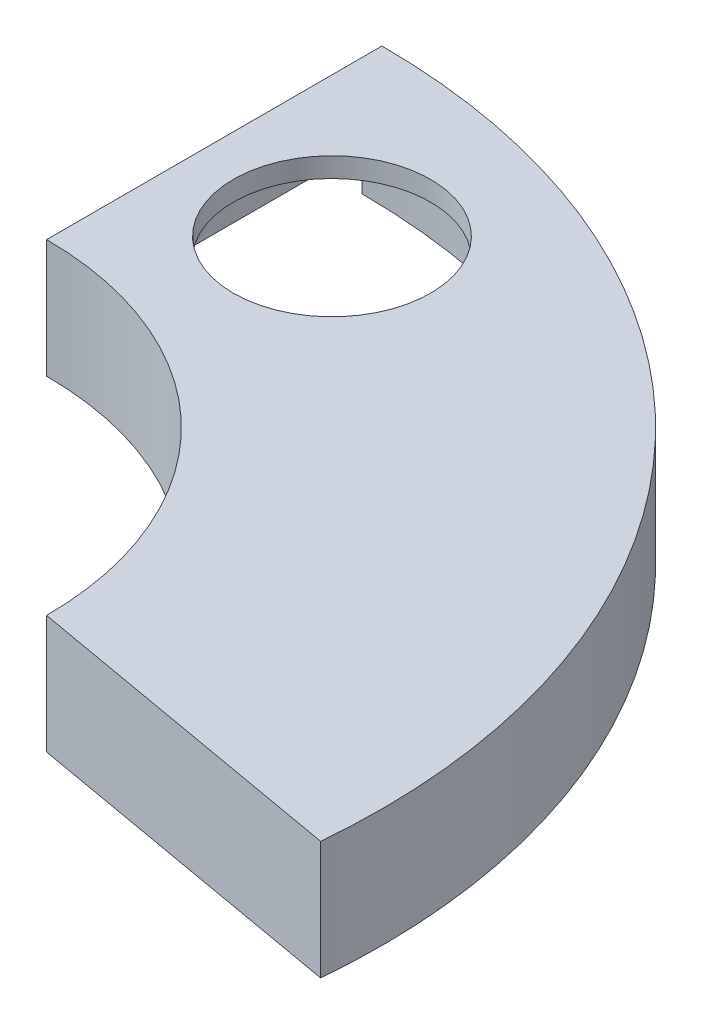
SolidWorks part; units mm, degrees
material "AISI 316 Chapa de acero inoxidable (SS)"
ref_plane "Alzado" through (0, 0, 0) normal (0, 0, 1) x (1, 0, 0)
ref_plane "Planta" through (0, 0, 0) normal (0, 1, 0) x (1, 0, 0)
ref_plane "Vista lateral" through (0, 0, 0) normal (1, 0, 0) x (0, 0, -1)
sketch "Croquis1" plane through (0, 0, 0) normal (0, 1, 0) x (1, 0, 0)
  line L0 (0, 165) -> (0, 335)
  line L1 (165, 0) -> (333.6771, -29.7423)
  arc A0 (333.6771, -29.7423) -> (0, 335) centre (0, 0) ccw
  arc A1 (165, 0) -> (0, 165) centre (0, 0) ccw
  circle A2 centre (70.8774, 238.7962) radius 50
  dimension "D1" = 670
  dimension "D2" = 330
  dimension "D4" = 100
  dimension "D3" = 100
extrude "Saliente-Extruir1" add sketch "Croquis1" along normal blind 10
sketch "Croquis2" plane through (0, 0, 0) normal (0, -1, 0) x (1, 0, 0)
  line L4 (10, -174.7141) -> (10, -324.8461)
  line L5 (324.5028, 17.9704) -> (174.797, -8.4268)
  line L6 (10, -174.7141) -> (10, -324.8461)
  line L7 (324.5028, 17.9704) -> (174.797, -8.4268)
  line L8 (0, -165) -> (0, -335)
  line L9 (333.6771, 29.7423) -> (165, 0)
  line L10 (0, -165) -> (0, -335)
  line L11 (333.6771, 29.7423) -> (165, 0)
  arc A4 (10, -174.7141) -> (174.797, -8.4268) centre (0, 0) ccw
  arc A5 (10, -324.8461) -> (324.5028, 17.9704) centre (0, 0) ccw
  arc A6 (10, -174.7141) -> (174.797, -8.4268) centre (0, 0) ccw
  arc A7 (10, -324.8461) -> (324.5028, 17.9704) centre (0, 0) ccw
  arc A8 (0, -165) -> (165, 0) centre (0, 0) ccw
  arc A9 (0, -335) -> (333.6771, 29.7423) centre (0, 0) ccw
  arc A10 (0, -165) -> (165, 0) centre (0, 0) ccw
  arc A11 (0, -335) -> (333.6771, 29.7423) centre (0, 0) ccw
  arc M9 (165, 0) -> (0, -165) centre (0, 0) cw
  line M10 (0, -165) -> (0, -335)
  arc M11 (0, -335) -> (333.6771, 29.7423) centre (0, 0) ccw
  line M12 (333.6771, 29.7423) -> (165, 0)
  dimension "D1" = 10
  dimension "D2" = 0
extrude "Saliente-Extruir2" add sketch "Croquis2" along normal blind 50 contours A7 L6 A6 L7 M12 M9 M10 M11 | A10 L11 A11 L10
sketch "Croquis3" plane through (0, -50, 0) normal (0, -1, 0) x (1, 0, 0)
  line L4 (324.5028, 17.9704) -> (174.797, -8.4268)
  line L5 (10, -174.7141) -> (10, -324.8461)
  line L6 (324.5028, 17.9704) -> (174.797, -8.4268)
  line L7 (10, -174.7141) -> (10, -324.8461)
  line L8 (333.6771, 29.7423) -> (165, 0)
  line L9 (0, -165) -> (0, -335)
  line L10 (333.6771, 29.7423) -> (165, 0)
  line L11 (0, -175) -> (0, -325)
  arc A2 (0, -175) -> (10, -174.7141) centre (0, 0) ccw
  arc A3 (0, -325) -> (10, -324.8461) centre (0, 0) ccw
  arc A4 (10, -174.7141) -> (174.797, -8.4268) centre (0, 0) ccw
  arc A5 (10, -324.8461) -> (324.5028, 17.9704) centre (0, 0) ccw
  arc A8 (0, -165) -> (165, 0) centre (0, 0) ccw
  arc A9 (0, -335) -> (333.6771, 29.7423) centre (0, 0) ccw
  arc A12 (324.5028, 17.9704) -> (323.7166, 28.8545) centre (0, 0) ccw
  arc A13 (174.797, -8.4268) -> (175, 0) centre (0, 0) ccw
  line M10 (10, -324.8461) -> (10, -174.7141)
  line M15 (0, -165) -> (0, -335)
  dimension "D1" = 10
  dimension "D2" = 0
extrude "Cortar-Extruir1" cut sketch "Croquis3" against normal blind 30 contours A3 A2 M15 M10
